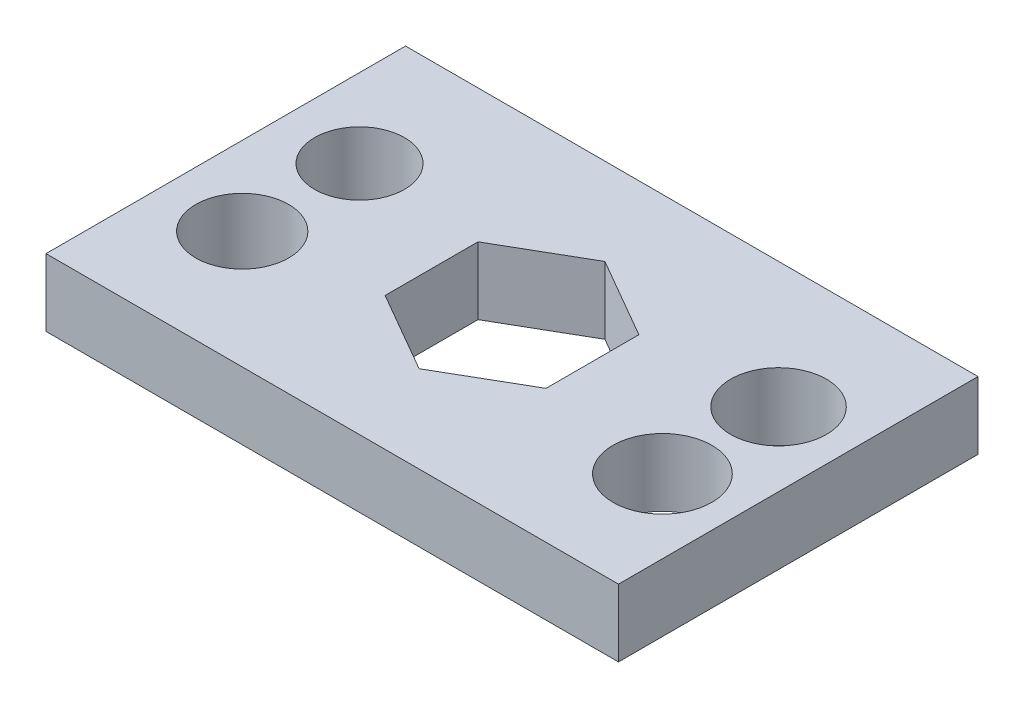
SolidWorks part; units mm, degrees
ref_plane "Front Plane" through (0, 0, 0) normal (0, 0, 1) x (1, 0, 0)
ref_plane "Top Plane" through (0, 0, 0) normal (0, 1, 0) x (1, 0, 0)
ref_plane "Right Plane" through (0, 0, 0) normal (1, 0, 0) x (0, 0, -1)
sketch "Sketch1" plane through (0, 0, 0) normal (0, 1, 0) x (1, 0, 0)
  line L1 (2.685, 1.5502) -> (0, 3.1004)
  line L2 (0, 3.1004) -> (-2.685, 1.5502)
  line L3 (-2.685, 1.5502) -> (-2.685, -1.5502)
  line L4 (-2.685, -1.5502) -> (0, -3.1004)
  line L5 (0, -3.1004) -> (2.685, -1.5502)
  line L6 (2.685, -1.5502) -> (2.685, 1.5502)
  line L7 (-9.5534, -6) -> (9.5534, -6)
  line L8 (-9.5534, -6) -> (-9.5534, 6)
  line L9 (-9.5534, 6) -> (9.5534, 6)
  line L10 (9.5534, -6) -> (9.5534, 6)
  line L11 (-9.5534, -6) -> (9.5534, 6) construction
  line L12 (-9.5534, 6) -> (9.5534, -6) construction
  circle A0 centre (0, 0) radius 2.685 construction
  circle A1 centre (-6.9258, 1.837) radius 1.5
  circle A2 centre (7.0989, 1.7973) radius 1.6
  circle A3 centre (7.0989, -2.0779) radius 1.65
  circle A4 centre (-6.9258, -2.0779) radius 1.55
  dimension "D1" = 5.37
  dimension "D3" = 3
  dimension "D4" = 3.2
  dimension "D5" = 3.3
  dimension "D6" = 3.1
  dimension "D2" = 12
extrude "Boss-Extrude1" add sketch "Sketch1" along normal blind 2.25
